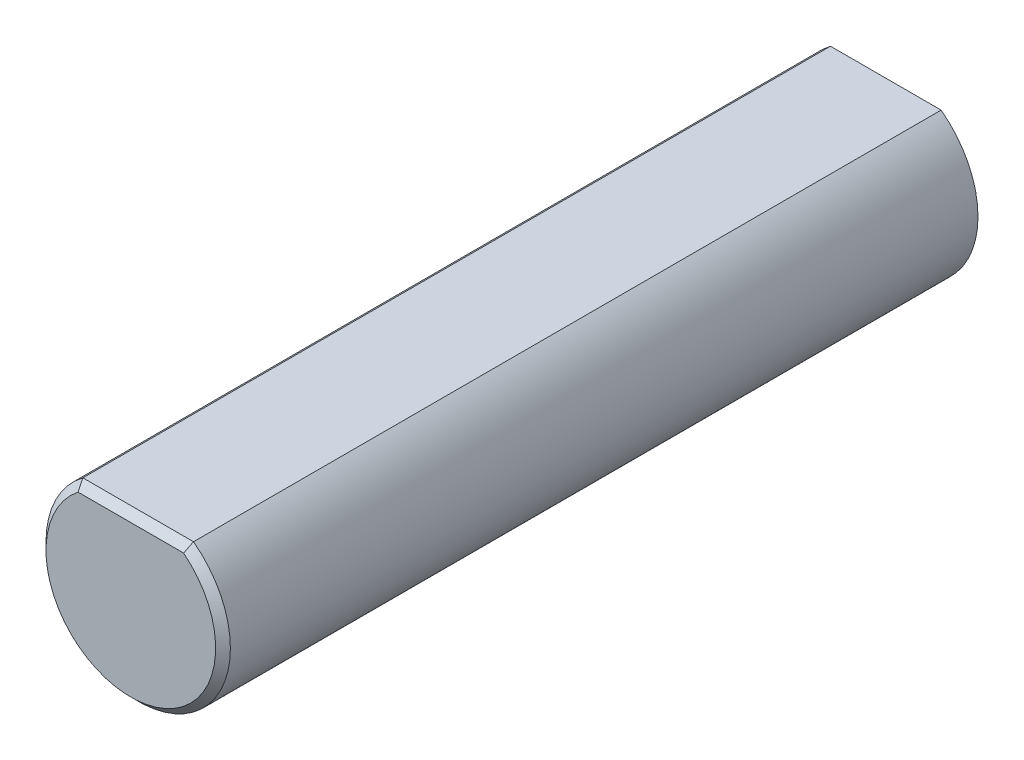
SolidWorks part; units mm, degrees
ref_plane "Front Plane" through (0, 0, 0) normal (0, 0, 1) x (1, 0, 0)
ref_plane "Top Plane" through (0, 0, 0) normal (0, 1, 0) x (1, 0, 0)
ref_plane "Right Plane" through (0, 0, 0) normal (1, 0, 0) x (0, 0, -1)
sketch "Sketch1" plane through (0, 0, 0) normal (0, 0, 1) x (1, 0, 0)
  line L1 (1.905, 2.54) -> (-1.905, 2.54)
  arc A0 (-1.905, 2.54) -> (1.905, 2.54) centre (0, 0) ccw
  dimension "D1" = 6.35
  dimension "D2" = 5.715
extrude "Boss-Extrude1" add sketch "Sketch1" along normal blind 26
chamfer "Chamfer1" distance 0.254 angle 45 2 edges at (0, 2.54, 26) (0, -3.175, 26)
